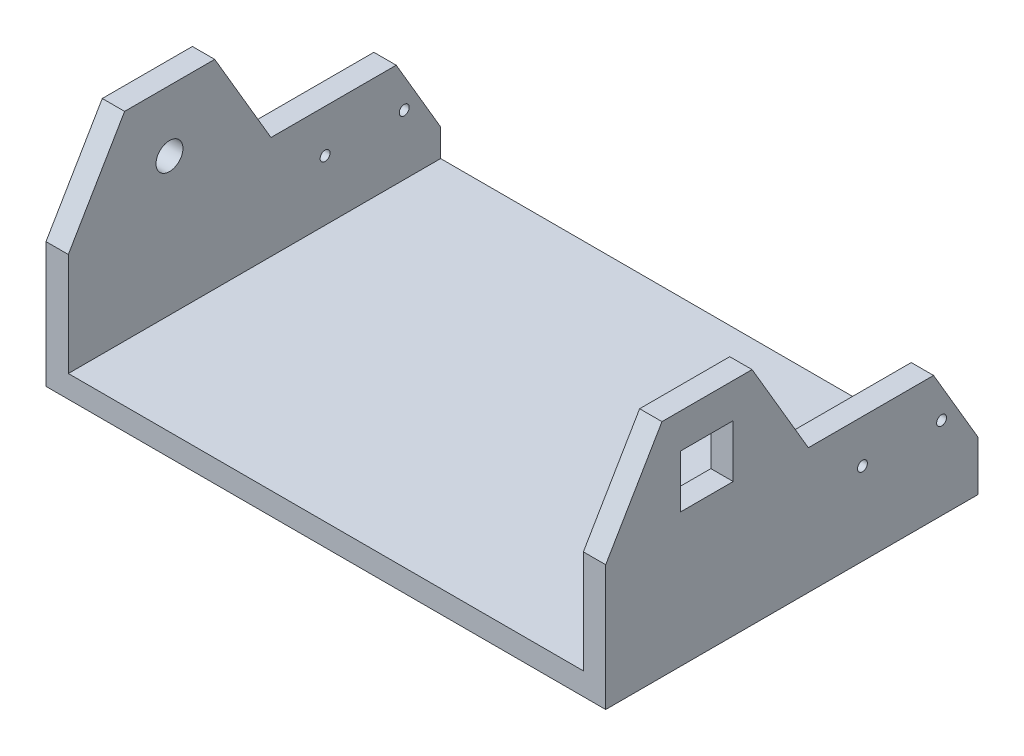
SolidWorks part; units mm, degrees
ref_plane "Front Plane" through (0, 0, 0) normal (0, 0, 1) x (1, 0, 0)
ref_plane "Top Plane" through (0, 0, 0) normal (0, 1, 0) x (1, 0, 0)
ref_plane "Right Plane" through (0, 0, 0) normal (1, 0, 0) x (0, 0, -1)
sketch "Sketch1" plane through (0, 0, 0) normal (0, 1, 0) x (1, 0, 0)
  line L0 (0, 300) -> (0, 0)
  line L1 (0, 0) -> (451, 0)
  line L2 (451, 300) -> (451, 0)
  line L7 (0, 300) -> (451, 300)
  line L11 (0, 0) -> (0, 540.7678) construction
  line L12 (0, 300) -> (480.3094, 300) construction
  line L13 (451, 300) -> (451, -222.7601) construction
  line L14 (451, 0) -> (-20.9058, 0) construction
  line L15 (0, 135) -> (480.3094, 135) construction
  line L16 (0, 165) -> (480.3094, 165) construction
extrude "Boss-Extrude6" add sketch "Sketch1" along normal blind 18
ref_plane "Plane3" through (451, 0, 0) normal (1, 0, 0) x (0, 0, -1)
sketch "Sketch4" plane through (451, 0, 0) normal (1, 0, 0) x (0, 0, -1)
  line L0 (0, 0) -> (0, 101.0596)
  line L1 (300, 0) -> (0, 0)
  line L2 (0, 101.0596) -> (45.3423, 178.2614)
  line L3 (45.3423, 178.2614) -> (117.955, 178.2614)
  line L4 (81.5, 129) -> (0, 101.0596) construction
  line L5 (81.5, 129) -> (163.2953, 101.0596) construction
  line L6 (117.955, 178.2614) -> (163.2953, 101.0596)
  line L7 (163.2953, 101.0596) -> (264.203, 101.0596)
  line L8 (264.203, 101.0596) -> (300, 40.1074)
  line L9 (300, 40.1074) -> (300, 0)
  line L10 (0, 101.0596) -> (163.2953, 101.0596) construction
  line L11 (60.25, 150.25) -> (102.75, 150.25)
  line L12 (60.25, 150.25) -> (60.25, 107.75)
  line L13 (60.25, 107.75) -> (102.75, 107.75)
  line L14 (102.75, 150.25) -> (102.75, 107.75)
  line L15 (60.25, 150.25) -> (102.75, 107.75) construction
  line L16 (60.25, 107.75) -> (102.75, 150.25) construction
  line L17 (300, 18) -> (270.64, 18) construction
  line L18 (0, 18) -> (300, 18) construction
  line L19 (300, 18) -> (206.89, 18) construction
  line L20 (206.89, 18) -> (206.89, 66.5) construction
  line L21 (270.64, 18) -> (270.64, 66.5) construction
  line L22 (0, 18) -> (0, 101.0596) construction
  circle A0 centre (206.89, 66.5) radius 4
  circle A1 centre (270.64, 66.5) radius 4
  point P1 (81.5, 129)
extrude "Boss-Extrude7" add sketch "Sketch4" against normal blind 18
ref_plane "Plane4" through (0, 0, 0) normal (-1, 0, 0) x (0, 0, 1)
sketch "Sketch5" plane through (0, 0, 0) normal (-1, 0, 0) x (0, 0, 1)
  line L0 (-300, 0) -> (-300, 40.1074)
  line L1 (-300, 0) -> (0, 0)
  line L2 (-300, 40.1074) -> (-264.203, 101.0596)
  line L3 (-264.203, 101.0596) -> (-163.2953, 101.0596)
  line L4 (-163.2953, 101.0596) -> (-117.955, 178.2614)
  line L5 (-117.955, 178.2614) -> (-45.3423, 178.2614)
  line L6 (-45.3423, 178.2614) -> (0, 101.0596)
  line L7 (0, 101.0596) -> (0, 0)
  line L8 (-300, 0) -> (-300, 40.1074) construction
  line L10 (-270.64, 40.1074) -> (-270.64, 66.5) construction
  line L11 (-163.2953, 101.0596) -> (-117.955, 101.0596) construction
  line L12 (-117.955, 101.0596) -> (-117.955, 178.2614) construction
  line L13 (-45.3423, 178.2614) -> (-45.3423, 101.0596) construction
  line L14 (-45.3423, 101.0596) -> (0, 101.0596) construction
  line L15 (-117.955, 178.2614) -> (-81.6487, 178.2614) construction
  line L16 (-81.6487, 178.2614) -> (-81.5, 129) construction
  line L17 (-117.955, 178.2614) -> (-81.6487, 178.2614) construction
  line L18 (-270.64, 40.1074) -> (-206.89, 40.1074) construction
  line L19 (-206.89, 40.1074) -> (-206.89, 66.5) construction
  circle A0 centre (-81.5, 129) radius 10.85
  circle A1 centre (-270.64, 66.5) radius 4
  circle A2 centre (-206.89, 66.5) radius 4
extrude "Boss-Extrude8" add sketch "Sketch5" against normal blind 18
